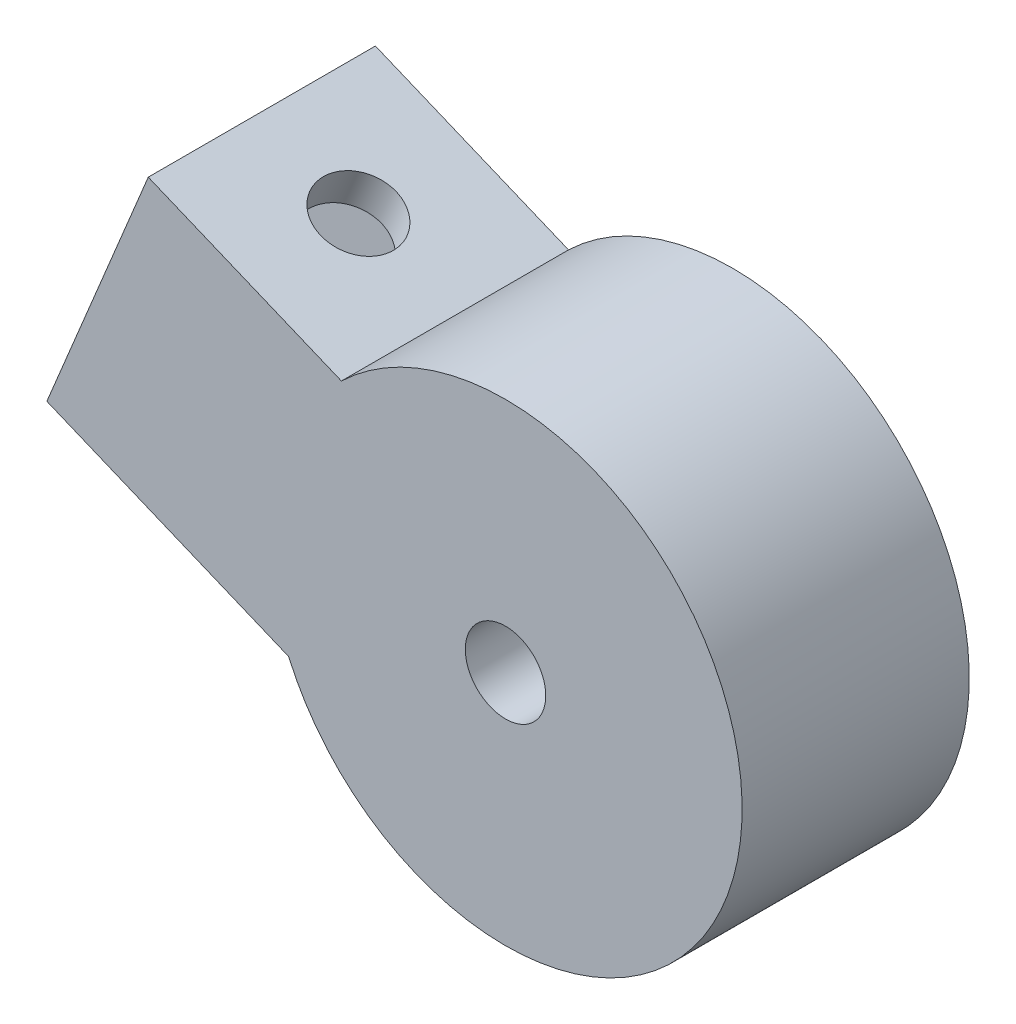
SolidWorks part; units mm, degrees
ref_plane "Front Plane" through (0, 0, 0) normal (0, 0, 1) x (1, 0, 0)
ref_plane "Top Plane" through (0, 0, 0) normal (0, 1, 0) x (1, 0, 0)
ref_plane "Right Plane" through (0, 0, 0) normal (1, 0, 0) x (0, 0, -1)
sketch "Sketch1" plane through (0, 0, 0) normal (0, 0, 1) x (1, 0, 0)
  line L0 (0, 0) -> (-12.5, 0) construction
  line L1 (0, 0) -> (-11.5485, -4.7835) construction
  line L3 (0, 0) -> (0, 10) construction
  line L12 (-20.7873, -8.6104) -> (-11.5485, -4.7835) construction
  line L16 (-20.7873, 8.6104) -> (-18.8739, 13.2298)
  line L20 (-18.8739, 13.2298) -> (-8.671, 9.0036)
  line L21 (-20.7873, 8.6104) -> (-24.2314, 0.2955)
  line L22 (-24.2314, 0.2955) -> (-11.4585, -4.9953)
  circle A3 centre (0, 0) radius 12.5
  circle A4 centre (0, 0) radius 10
  dimension "D1" = 25
  dimension "D3" = 22.5
  dimension "D2" = 20
  dimension "D4" = 10
extrude "Boss-Extrude2" add sketch "Sketch1" along normal blind 12 contours A3
sketch "Sketch2" plane through (0, 0, 0) normal (0, 0, 1) x (1, 0, 0)
  line L0 (-24.2314, 0.2955) -> (-11.4585, -4.9953) construction
  line L1 (-20.7873, 8.6104) -> (-24.2314, 0.2955) construction
  line L2 (-18.8739, 13.2298) -> (-8.671, 9.0036) construction
  line L3 (-20.7873, 8.6104) -> (-18.8739, 13.2298) construction
  line L4 (-24.2314, 0.2955) -> (-11.4585, -4.9953)
  line L5 (-20.7873, 8.6104) -> (-24.2314, 0.2955)
  line L6 (-18.8739, 13.2298) -> (-8.671, 9.0036)
  line L7 (-20.7873, 8.6104) -> (-18.8739, 13.2298)
  circle A0 centre (0, 0) radius 12.5 construction
  arc A1 (-8.671, 9.0036) -> (-11.4585, -4.9953) centre (0, 0) ccw
extrude "Boss-Extrude3" add sketch "Sketch2" along normal blind 12
sketch "Sketch3" plane through (-20.7873, 8.6104, 0) normal (-0.9239, 0.3827, 0) x (0, 0, 1)
  line L0 (12, 5) -> (0, 5) construction
  line L1 (2, 3) -> (10, 3)
  line L2 (2, 3) -> (2, -7)
  line L3 (2, -7) -> (10, -7)
  line L4 (10, 3) -> (10, -7)
  line L5 (12, -9) -> (0, -9) construction
  line L6 (0, 5) -> (0, -9) construction
  line L7 (12, 5) -> (12, -9) construction
  dimension "D1" = 2
  dimension "D2" = 2
  dimension "D3" = 2
  dimension "D4" = 2
extrude "Cut-Extrude1" cut sketch "Sketch3" against normal blind 10
sketch "Sketch4" plane through (1.9134, 4.6194, 0) normal (0.3827, 0.9239, 0) x (0.9239, -0.3827, 0)
  line L0 (-11.4564, -6) -> (-22.5, -6) construction
  line L1 (-11.4564, -12) -> (-11.4564, 0) construction
  line L2 (-22.5, -12) -> (-22.5, 0) construction
  line L3 (-16.9782, 0) -> (-16.9782, -12) construction
  line L4 (-11.4564, 0) -> (-22.5, 0) construction
  line L5 (-11.4564, -12) -> (-22.5, -12) construction
  circle A0 centre (-16.9782, -6) radius 2
extrude "Cut-Extrude2" cut sketch "Sketch4" against normal up to surface (14 mm away) up to face at (-17.845, -2.3499, 6)
sketch "Sketch5" plane through (0, 0, 12) normal (0, 0, 1) x (1, 0, 0)
  line L0 (0, 0) -> (0, 10) construction
  line L1 (0, 0) -> (10, 0) construction
  circle A7 centre (0, 0) radius 6.125
  point P17 (0, 0)
sketch "Sketch6" plane through (0, 0, 0) normal (0, 0, -1) x (-1, 0, 0)
  circle A0 centre (0, 0) radius 6.125 construction
  circle A1 centre (0, 0) radius 6.125
extrude "Cut-Extrude3" cut sketch "Sketch6" against normal blind 4
sketch "Sketch7" plane through (0, 0, 4) normal (0, 0, -1) x (-1, 0, 0)
  circle A0 centre (0, 0) radius 2.125
extrude "Cut-Extrude4" cut sketch "Sketch7" against normal through all
